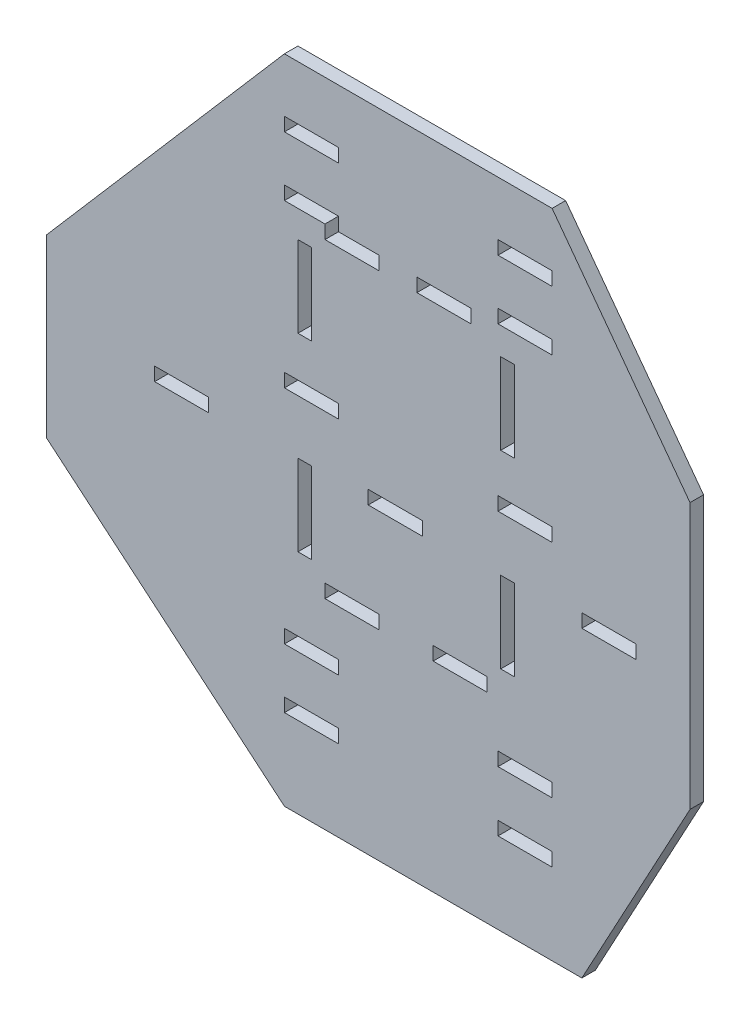
SolidWorks part; units mm, degrees
ref_plane "Front Plane" through (0, 0, 0) normal (0, 0, 1) x (1, 0, 0)
ref_plane "Top Plane" through (0, 0, 0) normal (0, 1, 0) x (1, 0, 0)
ref_plane "Right Plane" through (0, 0, 0) normal (1, 0, 0) x (0, 0, -1)
sketch "Sketch1" plane through (0, 0, 0) normal (0, 0, 1) x (1, 0, 0)
  line L0 (0, 46.3918) -> (0, -141.3147) construction
  line L1 (-45, 48.6826) -> (-45, -177.3121) construction
  line L2 (14, 45.4273) -> (14, -177.3121) construction
  line L3 (-14, 46.3918) -> (-14, -177.3121) construction
  line L4 (45, 44.6853) -> (45, -178.8013) construction
  line L5 (-89.0738, 44.6853) -> (96.7092, 44.6853) construction
  line L6 (-89.0738, 22.6853) -> (96.7092, 22.6853) construction
  line L7 (-89.0738, -37.3147) -> (96.7092, -37.3147) construction
  line L8 (-89.0738, -59.3147) -> (96.7092, -59.3147) construction
  line L9 (-93, -119.3147) -> (45, -119.3147) construction
  line L10 (-159.3206, -141.3147) -> (147.9491, -141.3147) construction
  line L11 (-93, 64.6853) -> (-93, -183.3147) construction
  line L12 (-45, 44.6853) -> (-65, 44.6853)
  line L13 (-45, 44.6853) -> (-45, 39.6853)
  line L14 (-45, 39.6853) -> (-65, 39.6853)
  line L15 (-65, 44.6853) -> (-65, 39.6853)
  line L16 (-45, 22.6853) -> (-65, 22.6853)
  line L17 (-45, 22.6853) -> (-45, 17.6853)
  line L18 (-45, 17.6853) -> (-65, 17.6853)
  line L19 (-65, 22.6853) -> (-65, 17.6853)
  line L20 (-45, -37.3147) -> (-65, -37.3147)
  line L21 (-45, -37.3147) -> (-45, -42.3147)
  line L22 (-45, -42.3147) -> (-65, -42.3147)
  line L23 (-65, -37.3147) -> (-65, -42.3147)
  line L24 (14, 44.6853) -> (34, 44.6853)
  line L25 (14, 44.6853) -> (14, 39.6853)
  line L26 (14, 39.6853) -> (34, 39.6853)
  line L27 (34, 44.6853) -> (34, 39.6853)
  line L28 (14, 22.6853) -> (34, 22.6853)
  line L29 (14, 22.6853) -> (14, 17.6853)
  line L30 (14, 17.6853) -> (34, 17.6853)
  line L31 (34, 22.6853) -> (34, 17.6853)
  line L32 (14, -37.3147) -> (34, -37.3147)
  line L33 (14, -37.3147) -> (14, -42.3147)
  line L34 (14, -42.3147) -> (34, -42.3147)
  line L35 (34, -37.3147) -> (34, -42.3147)
  line L36 (-14, -59.3147) -> (-34, -59.3147)
  line L37 (-14, -59.3147) -> (-14, -64.3147)
  line L38 (-14, -64.3147) -> (-34, -64.3147)
  line L39 (-34, -59.3147) -> (-34, -64.3147)
  line L40 (-45, -119.3147) -> (-65, -119.3147)
  line L41 (-45, -119.3147) -> (-45, -124.3147)
  line L42 (-45, -124.3147) -> (-65, -124.3147)
  line L43 (-65, -119.3147) -> (-65, -124.3147)
  line L44 (-45, -141.3147) -> (-65, -141.3147)
  line L45 (-45, -141.3147) -> (-45, -146.3147)
  line L46 (-45, -146.3147) -> (-65, -146.3147)
  line L47 (-65, -141.3147) -> (-65, -146.3147)
  line L56 (45, 59.5609) -> (45, -175.0822) construction
  line L57 (-20, 82.3507) -> (-20, -204.8348) construction
  line L58 (45, -59.3147) -> (65, -59.3147)
  line L59 (45, -59.3147) -> (45, -64.3147)
  line L60 (45, -64.3147) -> (65, -64.3147)
  line L61 (65, -59.3147) -> (65, -64.3147)
  line L62 (-93, -59.3147) -> (-113, -59.3147)
  line L63 (-93, -59.3147) -> (-93, -64.3147)
  line L64 (-93, -64.3147) -> (-113, -64.3147)
  line L65 (-113, -59.3147) -> (-113, -64.3147)
  line L66 (14, -124.1225) -> (34, -124.1225)
  line L67 (14, -124.1225) -> (14, -119.1225)
  line L68 (14, -119.1225) -> (34, -119.1225)
  line L69 (34, -124.1225) -> (34, -119.1225)
  line L70 (14, -141.3147) -> (34, -141.3147)
  line L71 (14, -141.3147) -> (14, -146.3147)
  line L72 (14, -146.3147) -> (34, -146.3147)
  line L73 (34, -141.3147) -> (34, -146.3147)
  line L74 (-142.6365, 17.6853) -> (103.5556, 17.6853) construction
  line L75 (-152.326, -102.3147) -> (102.1714, -102.3147) construction
  line L76 (20, 59.5609) -> (20, -180.7657) construction
  line L77 (-60, 71.3539) -> (-60, -167.5558) construction
  line L78 (85, -4.0539) -> (85, -102.3147)
  line L79 (-60, 7.6853) -> (-55, 7.6853)
  line L80 (-60, 7.6853) -> (-60, -22.3147)
  line L81 (-60, -22.3147) -> (-55, -22.3147)
  line L82 (-55, 7.6853) -> (-55, -22.3147)
  line L83 (-60, -92.3147) -> (-55, -92.3147)
  line L84 (-60, -92.3147) -> (-60, -62.3147)
  line L85 (-60, -62.3147) -> (-55, -62.3147)
  line L86 (-55, -92.3147) -> (-55, -62.3147)
  line L91 (20, 7.6853) -> (15, 7.6853)
  line L92 (20, 7.6853) -> (20, -22.3147)
  line L93 (20, -22.3147) -> (15, -22.3147)
  line L94 (15, 7.6853) -> (15, -22.3147)
  line L99 (20, -92.3147) -> (15, -92.3147)
  line L100 (20, -92.3147) -> (20, -62.3147)
  line L101 (20, -62.3147) -> (15, -62.3147)
  line L102 (15, -92.3147) -> (15, -62.3147)
  line L111 (10, -102.3147) -> (-10, -102.3147)
  line L112 (10, -102.3147) -> (10, -97.3147)
  line L113 (10, -97.3147) -> (-10, -97.3147)
  line L114 (-10, -102.3147) -> (-10, -97.3147)
  line L115 (-50, -102.3147) -> (-30, -102.3147)
  line L116 (-50, -102.3147) -> (-50, -97.3147)
  line L117 (-50, -97.3147) -> (-30, -97.3147)
  line L118 (-30, -102.3147) -> (-30, -97.3147)
  line L119 (-50, 17.6853) -> (-30, 17.6853)
  line L120 (-50, 17.6853) -> (-50, 12.6853)
  line L121 (-50, 12.6853) -> (-30, 12.6853)
  line L122 (-30, 17.6853) -> (-30, 12.6853)
  line L123 (4, 17.6853) -> (-16, 17.6853)
  line L124 (4, 17.6853) -> (4, 12.6853)
  line L125 (4, 12.6853) -> (-16, 12.6853)
  line L126 (-16, 17.6853) -> (-16, 12.6853)
  line L130 (-65, 64.6853) -> (-153, -37.3147)
  line L131 (34, 64.6853) -> (85, -4.0539)
  line L132 (85, -102.3147) -> (45, -176.3147)
  line L133 (-65, -176.3147) -> (-153, -102.3147)
  line L134 (-65, -176.3147) -> (45, -176.3147)
  line L135 (-153, -37.3147) -> (-153, -102.3147)
  line L136 (-65, 64.6853) -> (34, 64.6853)
  arc A0 (-93.4372, -176.3147) -> (-93, -176.5534) centre (-20, -42.3147) ccw
  point P85 (34, -143.8147)
  point P122 (4, 15.1853)
  dimension "D66" = 20
  dimension "D1" = 45
  dimension "D2" = 14
  dimension "D3" = 14
  dimension "D4" = 45
  dimension "D5" = 22
  dimension "D6" = 60
  dimension "D7" = 22
  dimension "D8" = 60
  dimension "D9" = 22
  dimension "D10" = 20
  dimension "D11" = 20
  dimension "D12" = 20
  dimension "D13" = 20
  dimension "D14" = 20
  dimension "D15" = 20
  dimension "D16" = 20
  dimension "D17" = 60
  dimension "D18" = 20
  dimension "D19" = 20
  dimension "D20" = 20
  dimension "D21" = 5
  dimension "D22" = 5
  dimension "D23" = 5
  dimension "D24" = 5
  dimension "D25" = 5
  dimension "D26" = 5
  dimension "D27" = 5
  dimension "D28" = 5
  dimension "D29" = 5
  dimension "D30" = 60
  dimension "D31" = 2.5
  dimension "D32" = 59
  dimension "D33" = 45
  dimension "D34" = 20
  dimension "D35" = 5
  dimension "D36" = 5
  dimension "D37" = 20
  dimension "D38" = 40
  dimension "D39" = 40
  dimension "D40" = 287.1855
  dimension "D41" = 10
  dimension "D42" = 30
  dimension "D43" = 5
  dimension "D44" = 10
  dimension "D45" = 30
  dimension "D46" = 5
  dimension "D47" = 10
  dimension "D48" = 30
  dimension "D49" = 5
  dimension "D50" = 10
  dimension "D51" = 30
  dimension "D52" = 5
  dimension "D53" = 223.4866
  dimension "D54" = 10
  dimension "D55" = 20
  dimension "D56" = 5
  dimension "D57" = 5
  dimension "D58" = 20
  dimension "D59" = 10
  dimension "D60" = 10
  dimension "D61" = 20
  dimension "D62" = 5
  dimension "D63" = 5
  dimension "D64" = 20
  dimension "D65" = 10
  dimension "D67" = 5
extrude "Boss-Extrude1" add sketch "Sketch1" along normal blind 5 contours L136 L130 L135 L133 L134 L132 L78 L131 L126 L123 L124 L125 L118 L115 L116 L117 L94 L91 L92 L93 L86 L83 L84 L85 L65 L62 L63 L64 L47 L44 L45 L46 L43 L40 L41 L42 L39 L36 L37 L38 L23 L20
